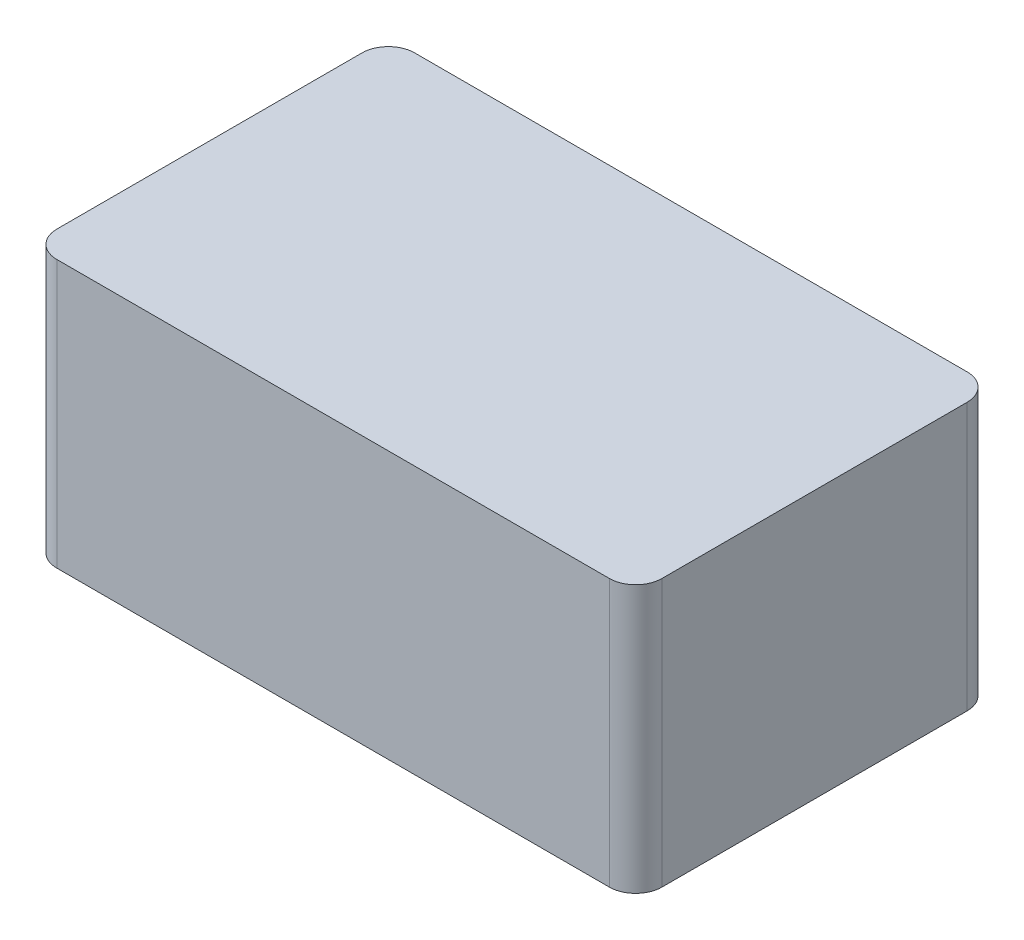
SolidWorks part; units mm, degrees
material "Custom Plastic"
ref_plane "Front Plane" through (0, 0, 0) normal (0, 0, 1) x (1, 0, 0)
ref_plane "Top Plane" through (0, 0, 0) normal (0, 1, 0) x (1, 0, 0)
ref_plane "Right Plane" through (0, 0, 0) normal (1, 0, 0) x (0, 0, -1)
sketch "Sketch2" plane through (0, 0, 0) normal (0, 1, 0) x (1, 0, 0)
  line L1 (-30.0488, 22.6829) -> (84.9512, 22.6829)
  line L2 (-30.0488, 22.6829) -> (-30.0488, -45.3171)
  line L3 (-30.0488, -45.3171) -> (84.9512, -45.3171)
  line L4 (84.9512, 22.6829) -> (84.9512, -45.3171)
  dimension "D1" = 115
  dimension "D2" = 68
extrude "Boss-Extrude1" add sketch "Sketch2" along normal blind 50.8
fillet "Fillet1" radius 5 4 edges at (84.9512, 25.4, -22.6829) (84.9512, 25.4, 45.3171) (-30.0488, 25.4, -22.6829) (-30.0488, 25.4, 45.3171)
